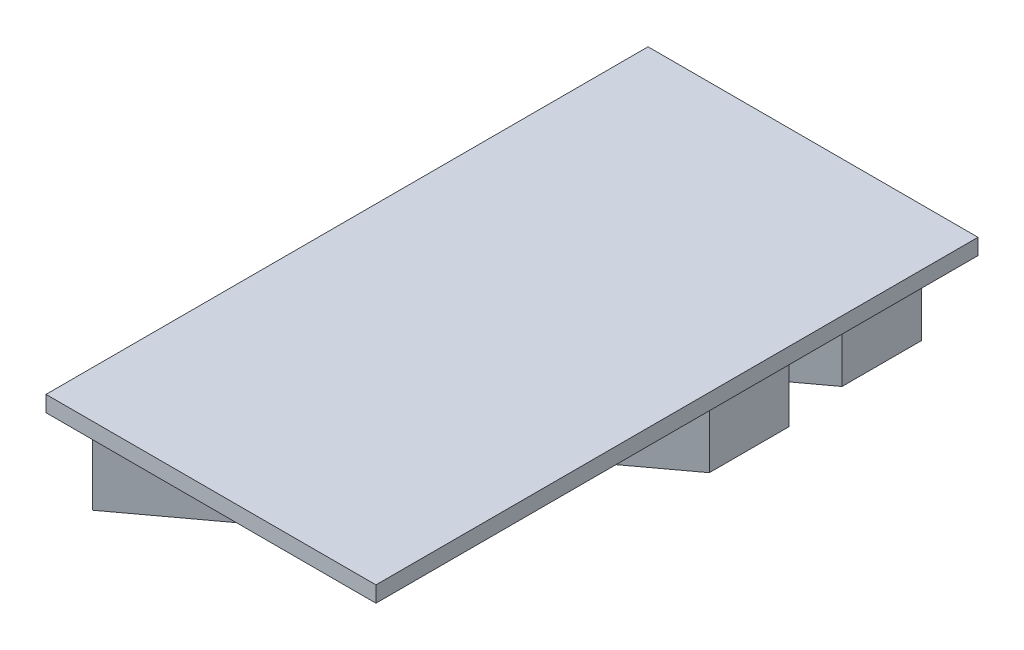
SolidWorks part; units mm, degrees
ref_plane "前视基准面" through (0, 0, 0) normal (0, 0, 1) x (1, 0, 0)
ref_plane "上视基准面" through (0, 0, 0) normal (0, 1, 0) x (1, 0, 0)
ref_plane "右视基准面" through (0, 0, 0) normal (1, 0, 0) x (0, 0, -1)
sketch "草图1" plane through (0, 0, 0) normal (0, 1, 0) x (1, 0, 0)
  line L0 (2.2502, 2.4555) -> (2.2502, 0.9542)
  line L1 (2.2502, 2.4555) -> (-3.0239, -1.4446)
  line L2 (2.2502, 0.9542) -> (-3.0239, -2.9459)
  line L3 (-3.0239, -1.4446) -> (-3.0239, -2.9459)
  line L4 (2.0936, 5.1162) -> (2.0936, 3.6148)
  line L5 (2.0936, 5.1162) -> (-0.3239, 3.3285)
  line L6 (2.0936, 3.6148) -> (-0.3239, 1.8272)
  line L7 (-0.3239, 3.3285) -> (-0.3239, 1.8272)
  line L8 (-0.5392, -2.189) -> (-0.5392, -3.6903)
  line L9 (-0.5392, -2.189) -> (-2.9567, -3.9766)
  line L10 (-0.5392, -3.6903) -> (-2.9567, -5.4779)
  line L11 (-2.9567, -3.9766) -> (-2.9567, -5.4779)
extrude "凸台-拉伸1" add sketch "草图1" along normal blind 1.5
sketch "草图2" plane through (0, 1.5, 0) normal (0, 1, 0) x (1, 0, 0)
  line L1 (-3.4867, 5.5353) -> (2.7379, 5.5353)
  line L2 (-3.4867, 5.5353) -> (-3.4867, -5.8227)
  line L3 (-3.4867, -5.8227) -> (2.7379, -5.8227)
  line L4 (2.7379, 5.5353) -> (2.7379, -5.8227)
  point P4 (3.2586, -3.8635)
  point P5 (2.7379, 5.5353)
extrude "凸台-拉伸2" add sketch "草图2" along normal blind 0.3
